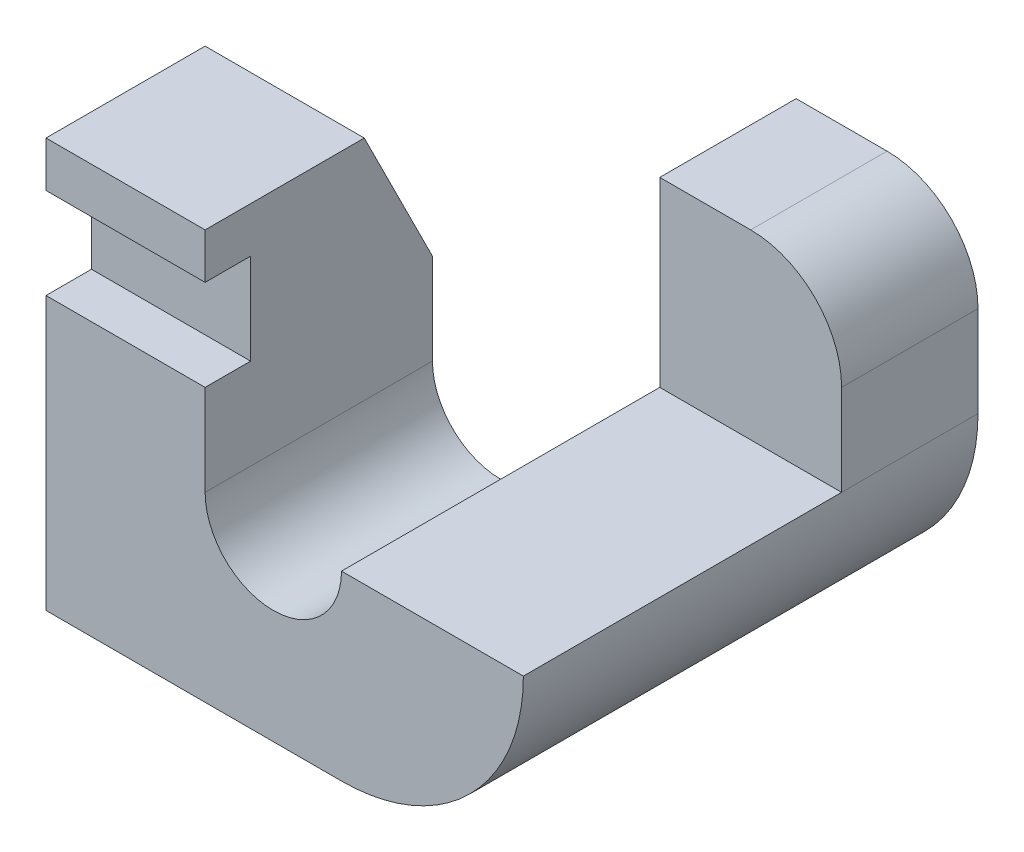
SolidWorks part; units mm, degrees
ref_plane "Front Plane" through (0, 0, 0) normal (0, 0, 1) x (1, 0, 0)
ref_plane "Top Plane" through (0, 0, 0) normal (0, 1, 0) x (1, 0, 0)
ref_plane "Right Plane" through (0, 0, 0) normal (1, 0, 0) x (0, 0, -1)
sketch "Sketch1" plane through (0, 0, 0) normal (0, 0, 1) x (1, 0, 0)
  line L0 (-64.0348, 29.6347) -> (-36.0348, 29.6347)
  line L1 (-64.0348, 29.6347) -> (-64.0348, -42.3653)
  line L2 (-64.0348, -42.3653) -> (-12.0348, -42.3653)
  line L4 (-36.0348, 29.6347) -> (-36.0348, -10.3653)
  line L5 (-12.0348, -10.3653) -> (-12.0348, 21.6347)
  line L6 (19.9652, -10.3653) -> (19.9652, 5.6347)
  line L7 (-12.0348, 21.6347) -> (3.9652, 21.6347)
  arc A0 (-12.0348, -42.3653) -> (19.9652, -10.3653) centre (-12.0348, -10.3653) ccw
  arc A1 (-36.0348, -10.3653) -> (-12.0348, -10.3653) centre (-24.0348, -10.3653) ccw
  arc A2 (3.9652, 21.6347) -> (19.9652, 5.6347) centre (3.9652, 5.6347) cw
extrude "Boss-Extrude1" add sketch "Sketch1" along normal blind 80
sketch "Sketch2" plane through (19.9652, 0, 0) normal (1, 0, 0) x (0, 0, -1)
  line L0 (-80, -10.3653) -> (-24, -10.3653)
  line L1 (-80, -10.3653) -> (0, -10.3653) construction
  line L2 (-24, -10.3653) -> (-24, 29.6347)
  line L3 (-80, 29.6347) -> (0, 29.6347) construction
  line L4 (-80, -10.3653) -> (-80, 29.6347)
  line L5 (-80, 29.6347) -> (-24, 29.6347)
extrude "Cut-Extrude1" cut sketch "Sketch2" against normal blind 32
sketch "Sketch3" plane through (0, 29.6347, 0) normal (0, 1, 0) x (1, 0, 0)
  line L2 (-12.0348, -80) -> (-12.0348, -24) construction
  line L3 (-12.0348, -40) -> (-64.0348, -40)
  line L5 (-64.0348, -80) -> (-64.0348, 0) construction
  line L6 (-39.6, 0) -> (39.6, 0) construction
  line L7 (-12.0348, -40) -> (-12.0348, 0) construction
  line L8 (-12.0348, -24) -> (-12.0348, 0) construction
  line L9 (-64.0348, -40) -> (-64.0348, 0)
  line L10 (-64.0348, 0) -> (-12.0348, 0)
  line L11 (-12.0348, 0) -> (-12.0348, -40)
extrude "Cut-Extrude2" cut sketch "Sketch3" against normal blind 100
sketch "Sketch4" plane through (-36.0348, 0, 0) normal (1, 0, 0) x (0, 0, -1)
  line L0 (-40, 29.6347) -> (-40, 5.6347)
  line L2 (-40, -10.3653) -> (-40, 29.6347) construction
  line L4 (-80, 29.6347) -> (-40, 29.6347) construction
  line L5 (-40, 5.6347) -> (-52, 29.6347)
  line L6 (-52, 29.6347) -> (-40, 29.6347)
extrude "Cut-Extrude3" cut sketch "Sketch4" against normal blind 100
sketch "Sketch5" plane through (0, 0, 0) normal (1, 0, 0) x (0, 0, -1)
  line L1 (-80, -10.3653) -> (-80, 29.6347) construction
  line L2 (-80, 21.6347) -> (-72, 21.6347)
  line L3 (-72, 21.6347) -> (-72, 5.6347)
  line L4 (-72, 5.6347) -> (-80, 5.6347)
  line L5 (-80, 5.6347) -> (-80, 21.6347)
extrude "Cut-Extrude4" cut sketch "Sketch5" against normal blind 100
